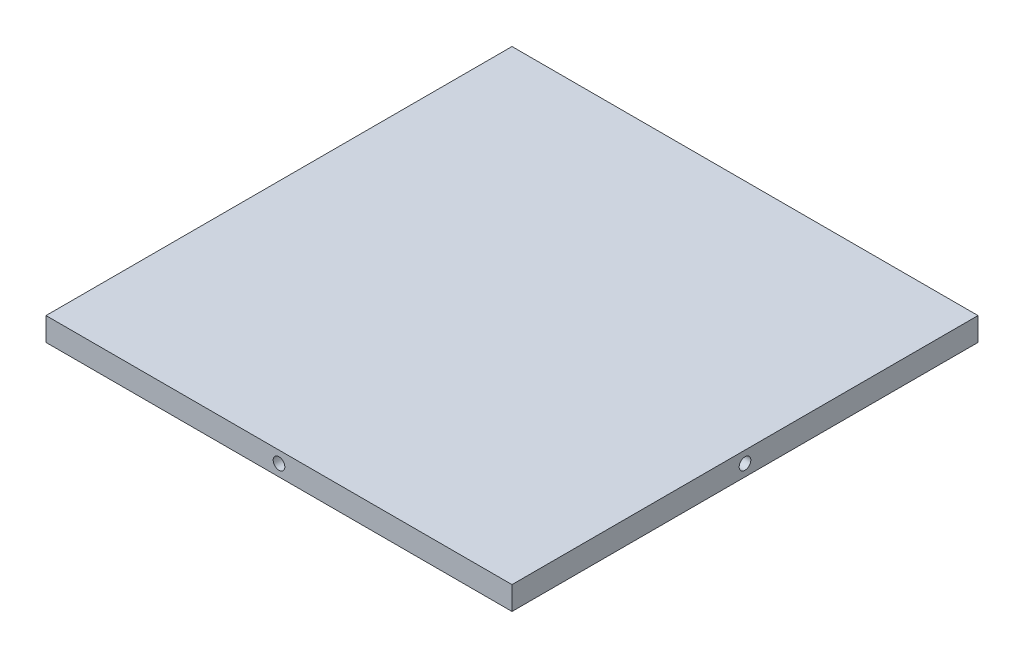
SolidWorks part; units mm, degrees
ref_plane "前视基准面" through (0, 0, 0) normal (0, 0, 1) x (1, 0, 0)
ref_plane "上视基准面" through (0, 0, 0) normal (0, 1, 0) x (1, 0, 0)
ref_plane "右视基准面" through (0, 0, 0) normal (1, 0, 0) x (0, 0, -1)
sketch "草图1" plane through (0, 0, 0) normal (0, 1, 0) x (1, 0, 0)
  line L1 (-60, -60) -> (60, -60)
  line L2 (-60, -60) -> (-60, 60)
  line L3 (-60, 60) -> (60, 60)
  line L4 (60, -60) -> (60, 60)
  point P0 (0, 0)
extrude "凸台-拉伸1" add sketch "草图1" along normal blind 6
sketch "草图2" plane through (60, 0, 0) normal (1, 0, 0) x (0, 0, -1)
  line L0 (-60, 6) -> (60, 0)
  line L1 (60, 0) -> (60, 6)
  line L2 (60, 6) -> (-60, 0)
  circle A0 centre (0, 3) radius 1.5
extrude "切除-拉伸1" cut sketch "草图2" against normal blind 16 contours A0
sketch "草图3" plane through (0, 0, -60) normal (0, 0, -1) x (-1, 0, 0)
  line L0 (-60, 6) -> (60, 0)
  line L1 (60, 0) -> (60, 6)
  line L2 (60, 6) -> (-60, 0)
  circle A0 centre (0, 3) radius 1.5
extrude "切除-拉伸4" cut sketch "草图3" against normal blind 16 contours A0
sketch "草图4" plane through (-60, 0, 0) normal (-1, 0, 0) x (0, 0, 1)
  line L0 (-60, 6) -> (60, 0)
  line L1 (60, 0) -> (60, 6)
  line L2 (60, 6) -> (-60, 0)
  circle A0 centre (0, 3) radius 1.5
extrude "切除-拉伸5" cut sketch "草图4" against normal blind 16 contours A0
sketch "草图5" plane through (0, 0, 60) normal (0, 0, 1) x (1, 0, 0)
  line L0 (-60, 6) -> (60, 0)
  line L1 (60, 0) -> (60, 6)
  line L2 (60, 6) -> (-60, 0)
  circle A0 centre (0, 3) radius 1.5
extrude "切除-拉伸6" cut sketch "草图5" against normal blind 16 contours A0
